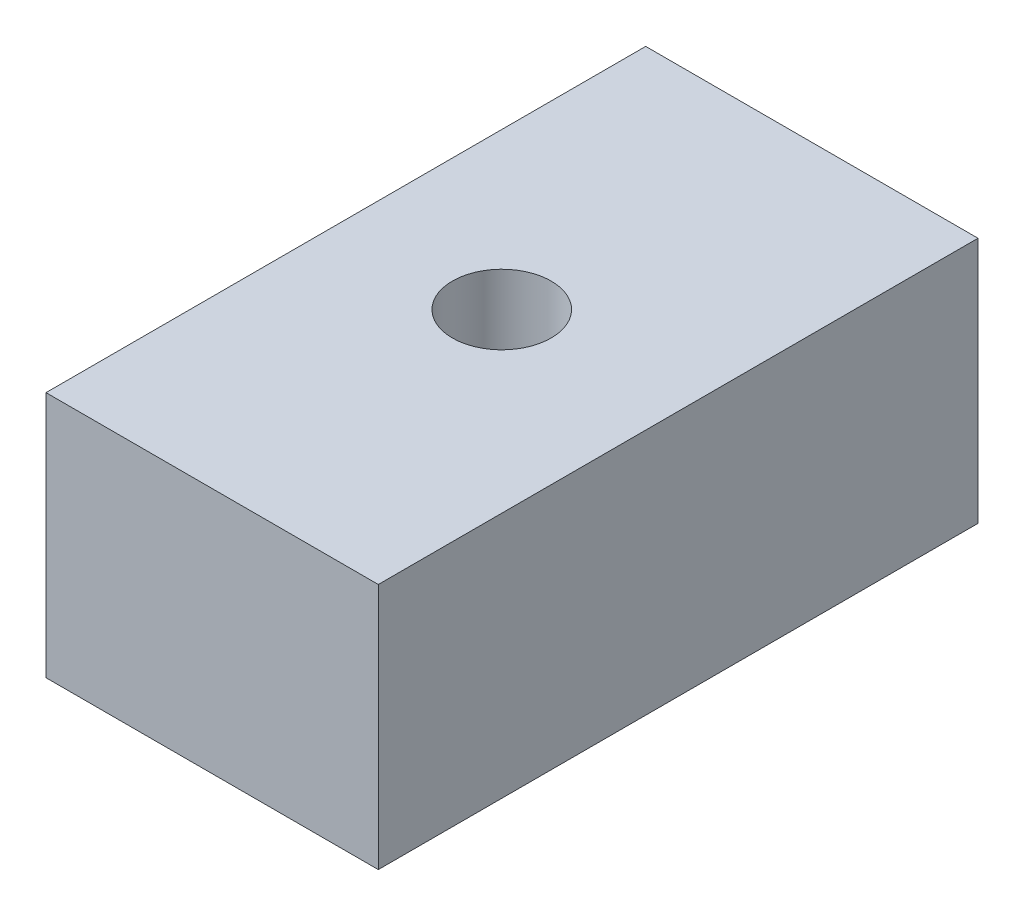
SolidWorks part; units mm, degrees
ref_plane "Plano frontal" through (0, 0, 0) normal (0, 0, 1) x (1, 0, 0)
ref_plane "Plano superior" through (0, 0, 0) normal (0, 1, 0) x (1, 0, 0)
ref_plane "Plano direito" through (0, 0, 0) normal (1, 0, 0) x (0, 0, -1)
sketch "Esboço1" plane through (0, 0, 0) normal (0, 1, 0) x (1, 0, 0)
  line L0 (4.42, 8.5) -> (9.42, 8.5) construction
  line L1 (0, 0) -> (9.42, 0)
  line L2 (0, 0) -> (0, 17)
  line L3 (0, 17) -> (9.42, 17)
  line L4 (9.42, 0) -> (9.42, 17)
  circle A0 centre (4.42, 8.5) radius 1.4
  dimension "D4" = 2.8
  dimension "D1" = 9.42
  dimension "D2" = 17
  dimension "D3" = 5
extrude "Ressalto-extrusão1" add sketch "Esboço1" along normal blind 7
